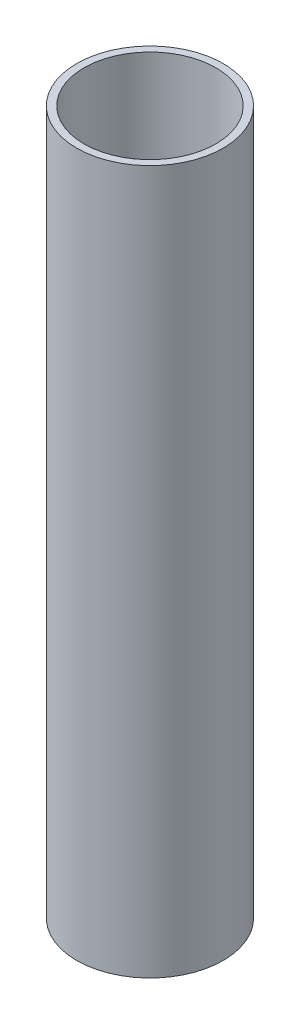
SolidWorks part; units mm, degrees
material "6061-T6 (SS)"
ref_plane "Front Plane" through (0, 0, 0) normal (0, 0, 1) x (1, 0, 0)
ref_plane "Top Plane" through (0, 0, 0) normal (0, 1, 0) x (1, 0, 0)
ref_plane "Right Plane" through (0, 0, 0) normal (1, 0, 0) x (0, 0, -1)
sketch "Sketch1" plane through (0, 0, 0) normal (0, 1, 0) x (1, 0, 0)
  circle A0 centre (0, 0) radius 31.75
  dimension "D1" = 63.5
extrude "Boss-Extrude1" add sketch "Sketch1" against normal blind 304.8
sketch "Sketch2" plane through (0, 0, 0) normal (0, 1, 0) x (1, 0, 0)
  circle A0 centre (0, 0) radius 28.575
  dimension "D1" = 57.15
extrude "Cut-Extrude1" cut sketch "Sketch2" against normal through all
